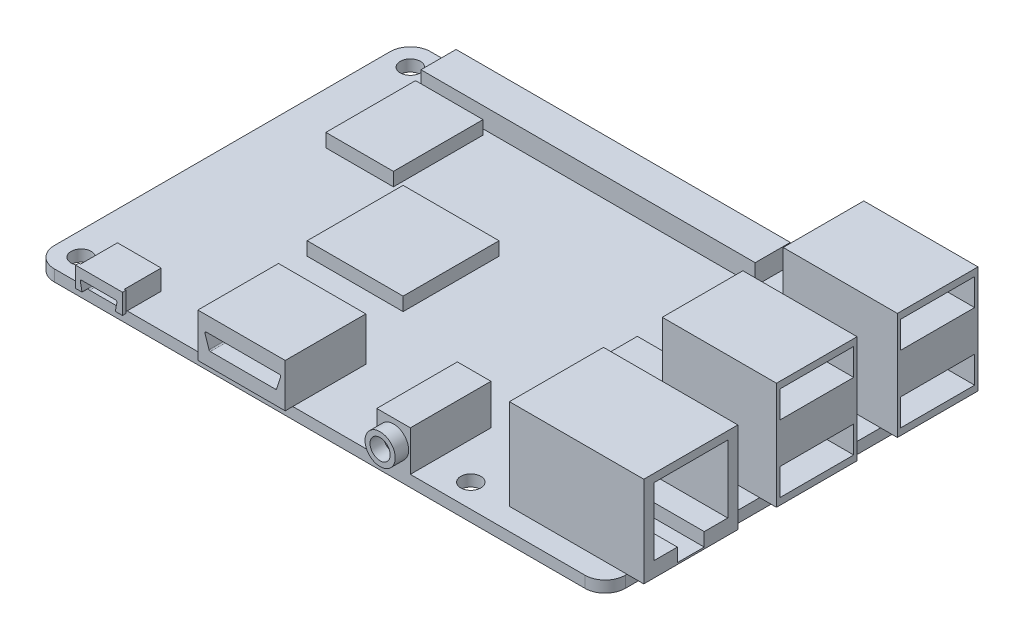
SolidWorks part; units mm, degrees
material "custom glass fiber"
ref_plane "Front" through (0, 0, 0) normal (0, 0, 1) x (1, 0, 0)
ref_plane "Top" through (0, 0, 0) normal (0, 1, 0) x (1, 0, 0)
ref_plane "Right" through (0, 0, 0) normal (1, 0, 0) x (0, 0, -1)
sketch "Sketch1" plane through (0, 0, 0) normal (0, 1, 0) x (1, 0, 0)
  line L1 (-39.5, 24.5) -> (39.5, 24.5)
  line L2 (-42.5, 21.5) -> (-42.5, -28.5)
  line L3 (-39.5, -31.5) -> (39.5, -31.5)
  line L4 (42.5, 21.5) -> (42.5, -28.5)
  arc A0 (39.5, -31.5) -> (42.5, -28.5) centre (39.5, -28.5) ccw
  arc A1 (-39.5, -31.5) -> (-42.5, -28.5) centre (-39.5, -28.5) cw
  arc A2 (-39.5, 24.5) -> (-42.5, 21.5) centre (-39.5, 21.5) ccw
  arc A3 (39.5, 24.5) -> (42.5, 21.5) centre (39.5, 21.5) cw
  circle A4 centre (-39, 21) radius 1.5
  circle A5 centre (-39, 21) radius 3
  circle A6 centre (-39, -28) radius 1.5
  circle A7 centre (-39, -28) radius 3
  circle A8 centre (19, 21) radius 1.5
  circle A9 centre (19, 21) radius 3
  circle A10 centre (19, -28) radius 1.5
  circle A11 centre (19, -28) radius 3
  point P7 (42.5, -31.5)
  point P10 (-42.5, -31.5)
  point P15 (42.5, 24.5)
  dimension "D5" = 3
  dimension "D8" = 6
  dimension "D9" = 3
  dimension "D10" = 6
  dimension "D11" = 3
  dimension "D16" = 6
  dimension "D17" = 3
  dimension "D19" = 3
  dimension "D20" = 6
  dimension "D1" = 56
  dimension "D2" = 85
  dimension "D3" = 42.5
  dimension "D4" = 24.5
  dimension "D6" = 3.5
  dimension "D7" = 3.5
  dimension "D12" = 3.5
  dimension "D13" = 3.5
  dimension "D14" = 58
  dimension "D15" = 3.5
  dimension "D18" = 58
  dimension "D21" = 3.5
extrude "Boss-Extrude1" add sketch "Sketch1" along normal blind 1.7 contours A3 L1 A2 L2 A1 L3 A0 L4 A11 A9 A7 A5 | A9 A8 | A5 A4 | A7 A6 | A11 A10
sketch "Sketch4" plane through (0, 1.7, 0) normal (0, 1, 0) x (1, 0, 0)
  line L1 (-34.875, 23.6848) -> (14.875, 23.6848)
  line L2 (-34.875, 23.6848) -> (-34.875, 18.4514)
  line L3 (-34.875, 18.4514) -> (14.875, 18.4514)
  line L4 (14.875, 23.6848) -> (14.875, 18.4514)
  point P4 (-10, 23.6848)
  dimension "D1" = 29
  dimension "D2" = 49.75
extrude "Boss-Extrude4" add sketch "Sketch4" along normal blind 3
sketch "Sketch6" plane through (0, 1.7, 0) normal (0, 1, 0) x (1, 0, 0)
  line L0 (-39.5, -31.5) -> (39.5, -31.5) construction
  line L1 (-40.5, 6.5) -> (-37.5, 6.5)
  line L2 (-40.5, 6.5) -> (-40.5, -13.5)
  line L3 (-40.5, -13.5) -> (-37.5, -13.5)
  line L4 (-37.5, 6.5) -> (-37.5, -13.5)
  line L5 (-42.5, 21.5) -> (-42.5, -28.5) construction
  line L6 (1, -10.7532) -> (4, -10.7532)
  line L7 (1, -10.7532) -> (1, -30.7532)
  line L8 (1, -30.7532) -> (4, -30.7532)
  line L9 (4, -10.7532) -> (4, -30.7532)
  point P4 (-40.5, -3.5)
  point P10 (-39, -13.5)
  point P16 (2.5, -30.7532)
  dimension "D1" = 28
  dimension "D2" = 20
  dimension "D3" = 3
  dimension "D4" = 45
  dimension "D5" = 3
  dimension "D6" = 20
sketch "Sketch7" plane through (0, 1.7, 0) normal (0, 1, 0) x (1, 0, 0)
  line L0 (-42.5, 21.5) -> (-42.5, -28.5) construction
  line L1 (-35.15, -26.4442) -> (-28.65, -26.4442)
  line L2 (-35.15, -26.4442) -> (-35.15, -31.9442)
  line L3 (-35.15, -31.9442) -> (-28.65, -31.9442)
  line L4 (-28.65, -26.4442) -> (-28.65, -31.9442)
  line L5 (-35.4, -31.9442) -> (-28.4, -31.9442)
  line L6 (-35.4, -31.9442) -> (-35.4, -32.4442)
  line L7 (-35.4, -32.4442) -> (-28.4, -32.4442)
  line L8 (-28.4, -31.9442) -> (-28.4, -32.4442)
  point P8 (-31.9, -31.9442)
  point P11 (-31.9, -32.4442)
  line M14 (-39.5, -31.5) -> (39.5, -31.5)
  dimension "D1" = 10.6
  dimension "D2" = 6.5
  dimension "D3" = 0.5
  dimension "D4" = 5.5
  dimension "D5" = 7
extrude "Boss-Extrude7" add sketch "Sketch7" along normal blind 3 contours L8 L5 L3 L6 L7 | L4 L1 L2 M14
sketch "Sketch8" plane through (0, 1.7, 0) normal (0, 1, 0) x (1, 0, 0)
  line L0 (-42.5, 21.5) -> (-42.5, -28.5) construction
  line L1 (-17, -20.6265) -> (-4, -20.6265)
  line L2 (-17, -20.6265) -> (-17, -32.6265)
  line L3 (-17, -32.6265) -> (-4, -32.6265)
  line L4 (-4, -20.6265) -> (-4, -32.6265)
  point P4 (-10.5, -32.6265)
  dimension "D1" = 32
  dimension "D2" = 12
  dimension "D3" = 13
extrude "Boss-Extrude8" add sketch "Sketch8" along normal blind 6.5
sketch "Sketch9" plane through (0, 1.7, 0) normal (0, 1, 0) x (1, 0, 0)
  line L0 (-39.5, -31.5) -> (39.5, -31.5) construction
  line L1 (8.5, -19.5) -> (13.5, -19.5)
  line L2 (8.5, -19.5) -> (8.5, -31.5)
  line L3 (8.5, -31.5) -> (13.5, -31.5)
  line L4 (13.5, -19.5) -> (13.5, -31.5)
  line L5 (-42.5, 21.5) -> (-42.5, -28.5) construction
  point P6 (11, -31.5)
  dimension "D1" = 53.5
  dimension "D2" = 5
  dimension "D3" = 12
extrude "Boss-Extrude9" add sketch "Sketch9" along normal blind 6
sketch "Sketch10" plane through (0, 1.7, 0) normal (0, 1, 0) x (1, 0, 0)
  line L0 (-39.5, -31.5) -> (39.5, -31.5) construction
  line L1 (25, -14.25) -> (45, -14.25)
  line L2 (25, -14.25) -> (25, -28.25)
  line L3 (25, -28.25) -> (45, -28.25)
  line L4 (45, -14.25) -> (45, -28.25)
  point P4 (45, -21.25)
  point P7 (35, -28.25)
  dimension "D1" = 10.25
  dimension "D2" = 14
  dimension "D3" = 16
  dimension "D4" = 20
extrude "Boss-Extrude10" add sketch "Sketch10" along normal blind 13.5
sketch "Sketch11" plane through (0, 1.7, 0) normal (0, 1, 0) x (1, 0, 0)
  line L0 (-39.5, -31.5) -> (39.5, -31.5) construction
  line L1 (28, 3.5) -> (45, 3.5)
  line L2 (28, 3.5) -> (28, -8.5)
  line L3 (28, -8.5) -> (45, -8.5)
  line L4 (45, 3.5) -> (45, -8.5)
  line L5 (28, 21.5) -> (45, 21.5)
  line L6 (28, 21.5) -> (28, 9.5)
  line L7 (28, 9.5) -> (45, 9.5)
  line L8 (45, 21.5) -> (45, 9.5)
  line L9 (45, -28.25) -> (45, -14.25) construction
  point P10 (45, -2.5)
  point P11 (45, 15.5)
  dimension "D1" = 29
  dimension "D2" = 47
  dimension "D3" = 12
  dimension "D4" = 12
  dimension "D5" = 17
  dimension "D6" = 17
extrude "Boss-Extrude11" add sketch "Sketch11" along normal blind 16
sketch "Sketch12" plane through (0, 1.7, 0) normal (0, 1, 0) x (1, 0, 0)
  line L1 (-34.875, 17.6449) -> (-24.8214, 17.6449)
  line L2 (-34.875, 17.6449) -> (-34.875, 4.3027)
  line L3 (-34.875, 4.3027) -> (-24.8214, 4.3027)
  line L4 (-24.8214, 17.6449) -> (-24.8214, 4.3027)
  line L5 (-22.2972, 3.2209) -> (-8.0174, 3.2209)
  line L6 (-22.2972, 3.2209) -> (-22.2972, -11.0589)
  line L7 (-22.2972, -11.0589) -> (-8.0174, -11.0589)
  line L8 (-8.0174, 3.2209) -> (-8.0174, -11.0589)
  line L9 (14.6, 1.19) -> (23.6, 1.19)
  line L10 (14.6, 1.19) -> (14.6, -7.81)
  line L11 (14.6, -7.81) -> (23.6, -7.81)
  line L12 (23.6, 1.19) -> (23.6, -7.81)
  line L13 (14.6, 1.19) -> (23.6, -7.81) construction
  line L14 (14.6, -7.81) -> (23.6, 1.19) construction
  line L15 (42.5, 9.5) -> (42.5, 3.5) construction
  line L16 (13.5, -31.5) -> (39.5, -31.5) construction
  point P8 (19.1, -3.31)
  dimension "D1" = 9
  dimension "D2" = 9
  dimension "D3" = 23.4
  dimension "D4" = 28.19
extrude "Boss-Extrude12" add sketch "Sketch12" along normal blind 2
sketch "Sketch13" plane through (0, 0, 31.5) normal (0, 0, 1) x (1, 0, 0)
  line L0 (-34.875, 4.7) -> (14.875, 4.7) construction
  circle A0 centre (11, 4.7) radius 2.25
  circle A1 centre (11, 4.7) radius 1.5
  dimension "D1" = 3
  dimension "D2" = 4.5
extrude "Boss-Extrude13" add sketch "Sketch13" along normal blind 2 contours A0 | A1
sketch "Sketch14" plane through (0, 0, 32.6265) normal (0, 0, 1) x (1, 0, 0)
  line L0 (-15.7503, 5.9838) -> (-4.8676, 5.9838)
  line L1 (-4.6777, 5.7212) -> (-5.2767, 3.9048)
  line L2 (-5.4667, 3.7674) -> (-15.1513, 3.7674)
  line L3 (-15.3412, 3.9048) -> (-15.9403, 5.7212)
  arc A0 (-5.4667, 3.7674) -> (-5.2767, 3.9048) centre (-5.4667, 3.9674) ccw
  arc A1 (-15.1513, 3.7674) -> (-15.3412, 3.9048) centre (-15.1513, 3.9674) cw
  arc A2 (-4.8676, 5.9838) -> (-4.6777, 5.7212) centre (-4.8676, 5.7838) cw
  arc A3 (-15.9403, 5.7212) -> (-15.7503, 5.9838) centre (-15.7503, 5.7838) cw
  dimension "D1" = 0.2
extrude "Cut-Extrude1" cut sketch "Sketch14" against normal blind 9
sketch "Sketch15" plane through (0, 0, 32.4442) normal (0, 0, 1) x (1, 0, 0)
  line L0 (-34.4753, 3.2042) -> (-29.4308, 3.2042)
  line L1 (-29.2344, 2.9665) -> (-29.471, 1.7328)
  line L2 (-34.6717, 2.9669) -> (-34.4376, 1.7331)
  line L5 (-34.2411, 1.5704) -> (-29.6674, 1.5704)
  arc A0 (-29.2344, 2.9665) -> (-29.4308, 3.2042) centre (-29.4308, 3.0042) ccw
  arc A1 (-29.6674, 1.5704) -> (-29.471, 1.7328) centre (-29.6674, 1.7704) ccw
  arc A2 (-34.2411, 1.5704) -> (-34.4376, 1.7331) centre (-34.2411, 1.7704) cw
  arc A3 (-34.6717, 2.9669) -> (-34.4753, 3.2042) centre (-34.4753, 3.0042) cw
  dimension "D1" = 0.2
extrude "Cut-Extrude2" cut sketch "Sketch15" against normal blind 5
sketch "Sketch16" plane through (45, 0, 0) normal (1, 0, 0) x (0, 0, -1)
  line L0 (-8.5, 17.7) -> (-8.5, 1.7) construction
  line L1 (-8, 6.7) -> (3, 6.7)
  line L2 (-8, 6.7) -> (-8, 2.7)
  line L3 (-8, 2.7) -> (3, 2.7)
  line L4 (3, 6.7) -> (3, 2.7)
  line L5 (3.5, 17.7) -> (3.5, 1.7) construction
  line L6 (-8.5, 1.7) -> (3.5, 1.7) construction
  line L7 (-8.5, 17.7) -> (3.5, 17.7) construction
  line L8 (-8, 16.7) -> (3, 16.7)
  line L9 (-8, 16.7) -> (-8, 12.7)
  line L10 (-8, 12.7) -> (3, 12.7)
  line L11 (3, 16.7) -> (3, 12.7)
  dimension "D1" = 4
  dimension "D2" = 0.5
  dimension "D3" = 0.5
  dimension "D4" = 1
  dimension "D5" = 4
  dimension "D6" = 1
extrude "Cut-Extrude3" cut sketch "Sketch16" against normal blind 10
sketch "Sketch17" plane through (45, 0, 0) normal (1, 0, 0) x (0, 0, -1)
  line L0 (9.5, 17.7) -> (9.5, 1.7) construction
  line L1 (10, 16.7) -> (21, 16.7)
  line L2 (10, 16.7) -> (10, 12.7)
  line L3 (10, 12.7) -> (21, 12.7)
  line L4 (21, 16.7) -> (21, 12.7)
  line L5 (10, 6.7) -> (21, 6.7)
  line L6 (10, 6.7) -> (10, 2.7)
  line L7 (10, 2.7) -> (21, 2.7)
  line L8 (21, 6.7) -> (21, 2.7)
  line L9 (21.5, 17.7) -> (21.5, 1.7) construction
  line L10 (9.5, 17.7) -> (21.5, 17.7) construction
  line L11 (21.5, 1.7) -> (9.5, 1.7) construction
  dimension "D1" = 0.5
  dimension "D2" = 4
  dimension "D3" = 0.5
  dimension "D4" = 1
  dimension "D5" = 4
  dimension "D6" = 1
  dimension "D7" = 0.5
  dimension "D8" = 0.5
extrude "Cut-Extrude4" cut sketch "Sketch17" against normal blind 10
sketch "Sketch18" plane through (45, 0, 0) normal (1, 0, 0) x (0, 0, -1)
  line L0 (-26.75, 14) -> (-26.75, 3.95)
  line L1 (-26.75, 3.95) -> (-23.25, 3.95)
  line L2 (-23.25, 3.95) -> (-23.25, 1.95)
  line L3 (-23.25, 1.95) -> (-19.25, 1.95)
  line L4 (-19.25, 1.95) -> (-19.25, 3.95)
  line L5 (-19.25, 3.95) -> (-15.75, 3.95)
  line L6 (-15.75, 3.95) -> (-15.75, 14)
  line L7 (-15.75, 14) -> (-26.75, 14)
  line L8 (-28.25, 15.2) -> (-28.25, 1.7) construction
  line L9 (-14.25, 15.2) -> (-14.25, 1.7) construction
  line L11 (-28.25, 15.2) -> (-14.25, 15.2) construction
  line L12 (-14.25, 1.7) -> (-28.25, 1.7) construction
  dimension "D1" = 1.5
  dimension "D2" = 1.5
  dimension "D3" = 3.5
  dimension "D4" = 3.5
  dimension "D5" = 1.2
  dimension "D6" = 0.25
  dimension "D7" = 2
  dimension "D8" = 2
extrude "Cut-Extrude5" cut sketch "Sketch18" against normal blind 12
sketch "Sketch21" plane through (35, 0, 0) normal (1, 0, 0) x (0, 0, -1)
  line L0 (3, 16.7) -> (-8, 16.7) construction
  line L1 (-7.85, 16.7) -> (2.85, 16.7)
  line L2 (-7.85, 16.7) -> (-7.85, 15.2)
  line L3 (-7.85, 15.2) -> (2.85, 15.2)
  line L4 (2.85, 16.7) -> (2.85, 15.2)
  line L5 (3, 12.7) -> (3, 16.7) construction
  line L6 (-8, 16.7) -> (-8, 12.7) construction
  dimension "D1" = 1.5
  dimension "D2" = 0.15
  dimension "D3" = 0.15
sketch "Sketch22" plane through (35, 0, 0) normal (1, 0, 0) x (0, 0, -1)
  line L0 (3, 6.7) -> (-8, 6.7) construction
  line L1 (-7.85, 6.7) -> (2.85, 6.7)
  line L2 (-7.85, 6.7) -> (-7.85, 5.2)
  line L3 (-7.85, 5.2) -> (2.85, 5.2)
  line L4 (2.85, 6.7) -> (2.85, 5.2)
  line L5 (-8, 6.7) -> (-8, 2.7) construction
  line L6 (3, 2.7) -> (3, 6.7) construction
  dimension "D1" = 1.5
  dimension "D2" = 0.15
  dimension "D3" = 0.15
sketch "Sketch23" plane through (35, 0, 0) normal (1, 0, 0) x (0, 0, -1)
  line L0 (21, 16.7) -> (10, 16.7) construction
  line L1 (10.15, 16.7) -> (20.85, 16.7)
  line L2 (10.15, 16.7) -> (10.15, 15.2)
  line L3 (10.15, 15.2) -> (20.85, 15.2)
  line L4 (20.85, 16.7) -> (20.85, 15.2)
  line L5 (10, 16.7) -> (10, 12.7) construction
  line L6 (21, 12.7) -> (21, 16.7) construction
  dimension "D1" = 1.5
  dimension "D2" = 0.15
  dimension "D3" = 0.15
sketch "Sketch24" plane through (35, 0, 0) normal (1, 0, 0) x (0, 0, -1)
  line L0 (21, 6.7) -> (10, 6.7) construction
  line L1 (10.15, 6.7) -> (20.85, 6.7)
  line L2 (10.15, 6.7) -> (10.15, 5.2)
  line L3 (10.15, 5.2) -> (20.85, 5.2)
  line L4 (20.85, 6.7) -> (20.85, 5.2)
  line L5 (10, 6.7) -> (10, 2.7) construction
  line L6 (21, 2.7) -> (21, 6.7) construction
  dimension "D1" = 1.5
  dimension "D2" = 0.15
  dimension "D3" = 0.15
extrude "Boss-Extrude18" [suppressed] add sketch "Sketch6" along normal blind 5.5
